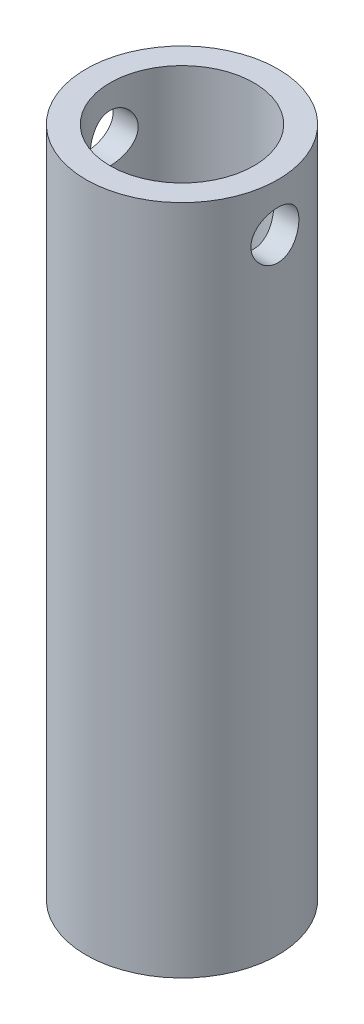
SolidWorks part; units mm, degrees
ref_plane "Front Plane" through (0, 0, 0) normal (0, 0, 1) x (1, 0, 0)
ref_plane "Top Plane" through (0, 0, 0) normal (0, 1, 0) x (1, 0, 0)
ref_plane "Right Plane" through (0, 0, 0) normal (1, 0, 0) x (0, 0, -1)
sketch "Sketch1" plane through (0, 0, 0) normal (0, 1, 0) x (1, 0, 0)
  circle A0 centre (0, 0) radius 12.7
  circle A1 centre (0, 0) radius 9.525
  dimension "D1" = 19.05
  dimension "D2" = 25.4
extrude "Boss-Extrude1" add sketch "Sketch1" along normal blind 88.9
sketch "Sketch2" plane through (0, 0, 0) normal (1, 0, 0) x (0, 0, -1)
  line L0 (0, 88.9) -> (0, 82.55) construction
  line L1 (9.525, 88.9) -> (-9.525, 88.9) construction
  circle A0 centre (0, 82.55) radius 3.175
  dimension "D1" = 6.35
  dimension "D2" = 6.35
extrude "Cut-Extrude1" cut sketch "Sketch2" against normal through all both and the other way through all
